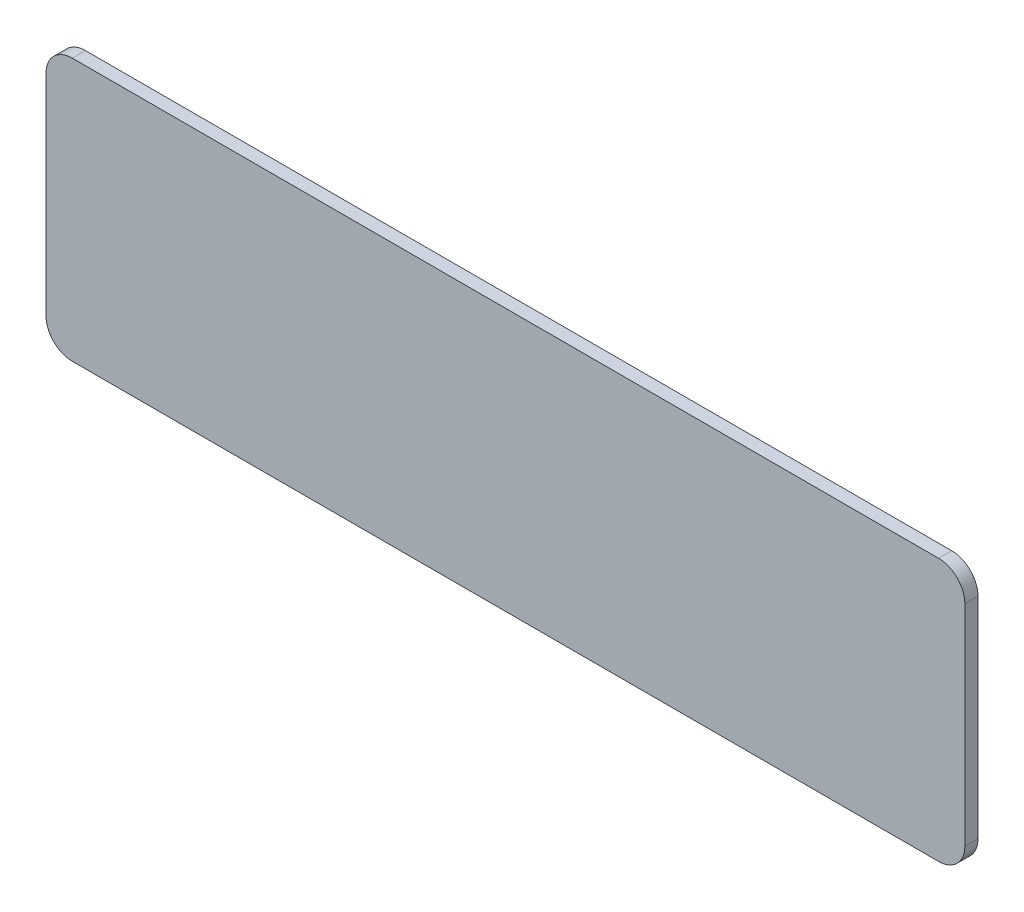
SolidWorks part; units mm, degrees
ref_plane "Front Plane" through (0, 0, 0) normal (0, 0, 1) x (1, 0, 0)
ref_plane "Top Plane" through (0, 0, 0) normal (0, 1, 0) x (1, 0, 0)
ref_plane "Right Plane" through (0, 0, 0) normal (1, 0, 0) x (0, 0, -1)
sketch "Sketch1" plane through (0, 0, 0) normal (0, 0, 1) x (1, 0, 0)
  line L0 (-46.63, 0) -> (244.89, 0) construction
  line L1 (-46.63, -25.35) -> (-46.63, 25.35) construction
  line L2 (244.89, 25.35) -> (244.89, -25.35) construction
  line L3 (-22.5, -25.35) -> (-46.63, -25.35) construction
  line L4 (-65.87, -50) -> (264.13, -50)
  line L5 (-75.87, -40) -> (-75.87, 40)
  line L6 (-65.87, 50) -> (264.13, 50)
  line L7 (274.13, -40) -> (274.13, 40)
  line L8 (-75.87, -50) -> (274.13, 50) construction
  line L9 (-75.87, 50) -> (274.13, -50) construction
  line L10 (22.5, -25.35) -> (-22.5, -25.35) construction
  line L11 (22.5, 25.35) -> (22.5, -25.35) construction
  line L12 (-22.5, 25.35) -> (22.5, 25.35) construction
  line L13 (-22.5, 25.35) -> (-46.63, 25.35) construction
  line L14 (-22.5, -25.35) -> (-46.63, -25.35)
  line L15 (22.5, -25.35) -> (-22.5, -25.35)
  line L16 (22.5, 25.35) -> (22.5, -25.35)
  line L17 (-22.5, 25.35) -> (22.5, 25.35)
  line L18 (-22.5, 25.35) -> (-46.63, 25.35)
  line L19 (-46.63, -25.35) -> (-46.63, 25.35)
  line L20 (51.63, -25.35) -> (27.5, -25.35) construction
  line L21 (96.63, -25.35) -> (51.63, -25.35) construction
  line L22 (96.63, 25.35) -> (96.63, -25.35) construction
  line L23 (51.63, 25.35) -> (96.63, 25.35) construction
  line L24 (51.63, 25.35) -> (27.5, 25.35) construction
  line L25 (27.5, -25.35) -> (27.5, 25.35) construction
  line L26 (51.63, -25.35) -> (27.5, -25.35)
  line L27 (96.63, -25.35) -> (51.63, -25.35)
  line L28 (96.63, 25.35) -> (96.63, -25.35)
  line L29 (51.63, 25.35) -> (96.63, 25.35)
  line L30 (51.63, 25.35) -> (27.5, 25.35)
  line L31 (27.5, -25.35) -> (27.5, 25.35)
  line L32 (125.76, -25.35) -> (101.63, -25.35) construction
  line L33 (170.76, -25.35) -> (125.76, -25.35) construction
  line L34 (170.76, 25.35) -> (170.76, -25.35) construction
  line L35 (125.76, 25.35) -> (170.76, 25.35) construction
  line L36 (125.76, 25.35) -> (101.63, 25.35) construction
  line L37 (101.63, -25.35) -> (101.63, 25.35) construction
  line L38 (125.76, -25.35) -> (101.63, -25.35)
  line L39 (170.76, -25.35) -> (125.76, -25.35)
  line L40 (170.76, 25.35) -> (170.76, -25.35)
  line L41 (125.76, 25.35) -> (170.76, 25.35)
  line L42 (125.76, 25.35) -> (101.63, 25.35)
  line L43 (101.63, -25.35) -> (101.63, 25.35)
  line L44 (175.76, -25.35) -> (175.76, 25.35) construction
  line L45 (199.89, -25.35) -> (175.76, -25.35) construction
  line L46 (244.89, -25.35) -> (199.89, -25.35) construction
  line L47 (199.89, 25.35) -> (244.89, 25.35) construction
  line L48 (199.89, 25.35) -> (175.76, 25.35) construction
  line L49 (199.89, -25.35) -> (175.76, -25.35)
  line L50 (244.89, -25.35) -> (199.89, -25.35)
  line L51 (244.89, 25.35) -> (244.89, -25.35)
  line L52 (199.89, 25.35) -> (244.89, 25.35)
  line L53 (199.89, 25.35) -> (175.76, 25.35)
  line L54 (175.76, -25.35) -> (175.76, 25.35)
  arc A0 (264.13, 50) -> (274.13, 40) centre (264.13, 40) cw
  arc A1 (264.13, -50) -> (274.13, -40) centre (264.13, -40) ccw
  arc A2 (-65.87, -50) -> (-75.87, -40) centre (-65.87, -40) cw
  arc A3 (-75.87, 40) -> (-65.87, 50) centre (-65.87, 40) cw
  point P6 (99.13, 0)
  dimension "D3" = 10
  dimension "D1" = 350
  dimension "D2" = 100
extrude "Boss-Extrude1" add sketch "Sketch1" against normal blind 5 contours L5 A3 L6 A0 L7 A1 L4 A2
